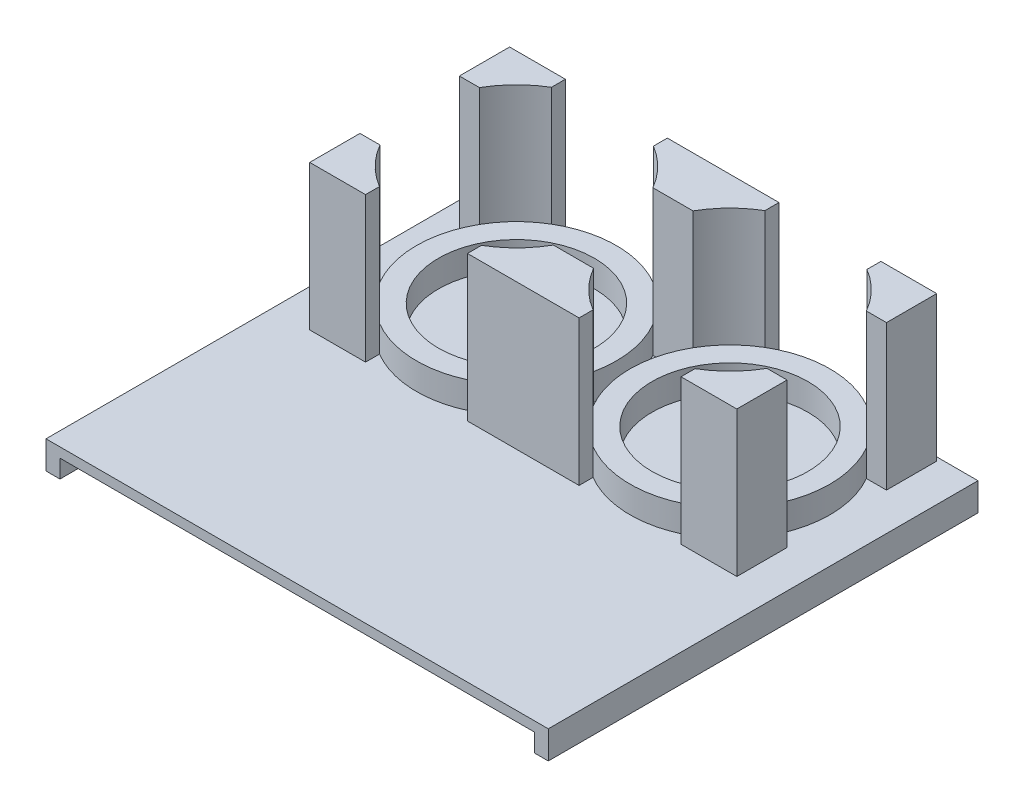
SolidWorks part; units mm, degrees
ref_plane "Front Plane" through (0, 0, 0) normal (0, 0, 1) x (1, 0, 0)
ref_plane "Top Plane" through (0, 0, 0) normal (0, 1, 0) x (1, 0, 0)
ref_plane "Right Plane" through (0, 0, 0) normal (1, 0, 0) x (0, 0, -1)
sketch "Sketch1" plane through (0, 0, 0) normal (0, 1, 0) x (1, 0, 0)
  line L0 (-42.5, 38.5) -> (42.5, 38.5)
  line L1 (0, -38.5) -> (0, 38.5) construction
  line L2 (-42.5, -38.5) -> (42.5, -38.5)
  line L3 (-42.5, 38.5) -> (-42.5, -38.5)
  line L4 (42.5, 38.5) -> (42.5, -38.5)
  point P3 (0, 38.5)
  point P7 (0, 0)
  point P11 (0, -38.5)
  dimension "D1" = 85
  dimension "D3" = 77
extrude "Boss-Extrude1" add sketch "Sketch1" along normal blind 1.75
sketch "Sketch3" plane through (0, 1.75, 0) normal (0, 1, 0) x (1, 0, 0)
  line L0 (-19.1333, 19.9281) -> (19.1333, 19.9281) construction
  line L2 (-1.263, 30.3299) -> (-0.4988, 30.3299)
  line L3 (20.6515, 40.5495) -> (-0.4988, 30.3299)
  line L5 (2.3974, 9.6528) -> (17.6152, -0.6933)
  line L6 (17.6152, -0.6933) -> (36.2329, 8.3027)
  line L7 (36.2329, 8.3027) -> (37.7511, 28.9241)
  line L8 (37.7511, 28.9241) -> (20.6515, 40.5495)
  line L9 (-19.2063, 40.6052) -> (-37.0767, 30.2034)
  line L10 (-37.0767, 30.2034) -> (-37.0037, 9.5264)
  line L11 (-37.0037, 9.5264) -> (-19.0603, -0.749)
  line L12 (-19.0603, -0.749) -> (-1.1899, 9.6528)
  line L13 (-1.1899, 9.6528) -> (-1.263, 30.3299)
  line L14 (-1.263, 30.3299) -> (-19.2063, 40.6052)
  line L15 (-1.1899, 9.6528) -> (2.3974, 9.6528)
  line L16 (0.8218, 15.0915) -> (-0.7932, -6.845) [skipped]
  circle A0 centre (19.1333, 19.9281) radius 17.907
  circle A1 centre (-19.1333, 19.9281) radius 17.907
  circle A2 centre (-19.1333, 19.9281) radius 13.97
  circle A3 centre (19.1333, 19.9281) radius 13.97
  circle A4 centre (19.1333, 19.9281) radius 17.907 construction
  circle A5 centre (-19.1333, 19.9281) radius 17.907 construction
  point P4 (0, 0)
  dimension "D1" = 35.814
  dimension "D3" = 27.94
extrude "Boss-Extrude3" add sketch "Sketch3" along normal blind 4.7625
sketch "Sketch4" plane through (0, 1.75, 0) normal (0, 1, 0) x (1, 0, 0)
  line L0 (-19.1333, 37.8351) -> (19.1333, 37.8351) construction
  line L1 (0, 37.8351) -> (-10, 37.8351)
  line L2 (-10, 37.8351) -> (-10, 35.3308)
  line L3 (0, 37.8351) -> (10, 37.8351)
  line L4 (10, 37.8351) -> (10, 35.3308)
  line L5 (-1.2263, 19.9281) -> (16.6975, 19.9281) construction
  line L6 (-3.5987, 28.8351) -> (3.5987, 28.8351)
  line L7 (-3.5987, 11.0211) -> (3.5987, 11.0211)
  line L8 (10, 2.0211) -> (10, 4.5254)
  line L9 (0, 2.0211) -> (10, 2.0211)
  line L10 (-10, 2.0211) -> (-10, 4.5254)
  line L11 (0, 2.0211) -> (-10, 2.0211)
  line L12 (0, 37.8351) -> (0, 28.8351)
  line L13 (0, 11.0211) -> (0, 2.0211)
  line L14 (-19.1333, 37.8351) -> (-19.1333, 19.9281) construction
  line L15 (19.1333, 37.8351) -> (19.1333, 19.9281) construction
  line L16 (-38.2667, 11.0211) -> (-38.2667, 2.0211)
  line L17 (-38.2667, 2.0211) -> (-28.2667, 2.0211)
  line L18 (-28.2667, 2.0211) -> (-28.2667, 4.5254)
  line L19 (-38.2667, 37.8351) -> (-38.2667, 28.8351)
  line L20 (-38.2667, 37.8351) -> (-28.2667, 37.8351)
  line L21 (-28.2667, 37.8351) -> (-28.2667, 35.3308)
  line L22 (-38.2667, 28.8351) -> (-34.668, 28.8351)
  line L23 (-38.2667, 11.0211) -> (-34.668, 11.0211)
  line L24 (28.2667, 2.0211) -> (28.2667, 4.5254)
  line L25 (38.2667, 2.0211) -> (28.2667, 2.0211)
  line L26 (38.2667, 11.0211) -> (38.2667, 2.0211)
  line L27 (38.2667, 28.8351) -> (34.668, 28.8351)
  line L28 (28.2667, 37.8351) -> (28.2667, 35.3308)
  line L29 (38.2667, 37.8351) -> (28.2667, 37.8351)
  line L30 (38.2667, 37.8351) -> (38.2667, 28.8351)
  line L31 (38.2667, 11.0211) -> (34.668, 11.0211)
  circle A0 centre (-19.1333, 19.9281) radius 17.907 construction
  circle A1 centre (19.1333, 19.9281) radius 17.907 construction
  arc A2 (10, 35.3308) -> (3.5987, 28.8351) centre (19.1333, 19.9281) ccw
  circle A3 centre (-19.1333, 19.9281) radius 17.907 construction
  circle A4 centre (19.1333, 19.9281) radius 17.907 construction
  arc A5 (-3.5987, 28.8351) -> (-10, 35.3308) centre (-19.1333, 19.9281) ccw
  arc A6 (-3.5987, 11.0211) -> (-10, 4.5254) centre (-19.1333, 19.9281) cw
  arc A7 (10, 4.5254) -> (3.5987, 11.0211) centre (19.1333, 19.9281) cw
  arc A8 (-34.668, 11.0211) -> (-28.2667, 4.5254) centre (-19.1333, 19.9281) ccw
  arc A9 (-34.668, 28.8351) -> (-28.2667, 35.3308) centre (-19.1333, 19.9281) cw
  arc A10 (34.668, 11.0211) -> (28.2667, 4.5254) centre (19.1333, 19.9281) cw
  arc A11 (34.668, 28.8351) -> (28.2667, 35.3308) centre (19.1333, 19.9281) ccw
  point P0 (0, 28.8351)
  point P4 (0, 0)
  point P29 (0, 11.0211)
  circle M6 centre (19.1333, 19.9281) radius 17.907
  circle M7 centre (-19.1333, 19.9281) radius 17.907
  dimension "D3" = 9
  dimension "D2" = 10
extrude "Boss-Extrude7" add sketch "Sketch4" along normal blind 26 contours L19 L22 L21 L20 M7 | L23 L16 L17 L18 M7 | L13 L7 L10 L11 M7 | L7 L13 L9 L8 M6 | L12 L1 L2 L6 M7 | L3 L12 L6 L4 M6 | L30 L29 L28 L27 M6 | L26 L31 L24 L25 M6
sketch "Sketch6" plane through (-42.5, 0, 0) normal (-1, 0, 0) x (0, 0, 1)
  line L0 (-38.5, 1.75) -> (-38.5, -3.25)
  line L1 (38.5, 1.75) -> (38.5, -3.25)
  line L2 (-38.5, 1.75) -> (38.5, 1.75) construction
  line L3 (-38.5, 1.75) -> (38.5, 1.75)
  line L4 (-38.5, -3.25) -> (38.5, -3.25)
  dimension "D1" = 5
extrude "Boss-Extrude8" add sketch "Sketch6" along normal blind 2.5
mirror "Mirror1" about plane through (0, 0, 0) normal (1, 0, 0) of "Boss-Extrude8"
sketch "Sketch7" plane through (0, 1.75, 0) normal (0, 1, 0) x (1, 0, 0)
  line L0 (-38.2667, 37.8351) -> (38.2667, 37.8351) construction
  line L1 (38.2667, 37.8351) -> (38.2667, 2.0211) construction
  line L2 (38.2667, 2.0211) -> (-38.2667, 2.0211) construction
  line L3 (-38.2667, 2.0211) -> (-38.2667, 37.8351) construction
  line L4 (-19.1333, 33.8981) -> (-19.1333, 19.9281) construction
  line L5 (-38.2667, 19.9281) -> (-19.1333, 19.9281) construction
  line L6 (19.1333, 33.8981) -> (19.1333, 19.9281) construction
  line L7 (-19.1333, 19.9281) -> (19.1333, 19.9281) construction
  circle A2 centre (-19.1333, 19.9281) radius 13.97 construction
  circle A3 centre (-19.1333, 19.9281) radius 13.97 construction
  circle A4 centre (19.1333, 19.9281) radius 13.97 construction
  circle A5 centre (19.1333, 19.9281) radius 13.97 construction
  dimension "D1" = 35.814
  dimension "D2" = 76.5333
  dimension "D3" = 19.1333
  dimension "D4" = 38.2667
